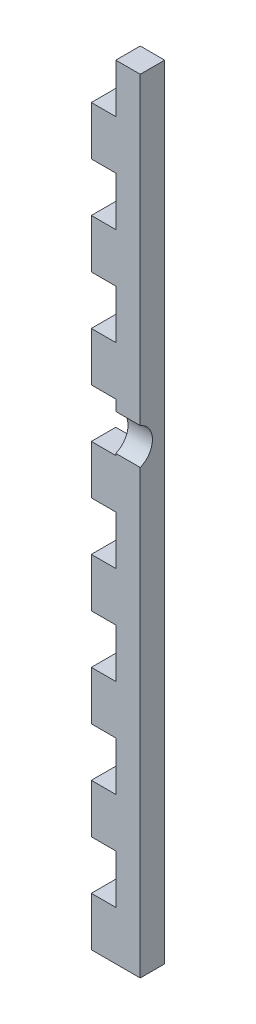
SolidWorks part; units mm, degrees
material "Balsa"
ref_plane "Alzado" through (0, 0, 0) normal (0, 0, 1) x (1, 0, 0)
ref_plane "Planta" through (0, 0, 0) normal (0, 1, 0) x (1, 0, 0)
ref_plane "Vista lateral" through (0, 0, 0) normal (1, 0, 0) x (0, 0, -1)
sketch "Croquis1" plane through (0, 0, 0) normal (0, 0, 1) x (1, 0, 0)
  line L0 (-10.5031, 53.1111) -> (-10.5031, 43.1111)
  line L1 (-10.5031, 73.1111) -> (-0.5031, 73.1111)
  line L2 (-10.5031, 73.1111) -> (-10.5031, -86.8889)
  line L3 (-10.5031, -86.8889) -> (-0.5031, -86.8889)
  line L4 (-0.5031, 73.1111) -> (-0.5031, -86.8889)
  line L5 (-10.5031, 73.1111) -> (-5.5031, 73.1111)
  line L6 (-10.5031, 73.1111) -> (-10.5031, 63.1111)
  line L7 (-10.5031, 63.1111) -> (-5.5031, 63.1111)
  line L8 (-5.5031, 73.1111) -> (-5.5031, 63.1111)
  line L9 (-10.5031, 53.1111) -> (-5.5031, 53.1111)
  line L10 (-5.5031, 53.1111) -> (-5.5031, 43.1111)
  line L11 (-10.5031, 43.1111) -> (-5.5031, 43.1111)
  line L12 (-10.5031, 33.1111) -> (-10.5031, 23.1111)
  line L13 (-10.5031, 33.1111) -> (-5.5031, 33.1111)
  line L14 (-5.5031, 33.1111) -> (-5.5031, 23.1111)
  line L15 (-10.5031, 23.1111) -> (-5.5031, 23.1111)
  line L16 (-10.5031, 13.1111) -> (-10.5031, 3.1111)
  line L17 (-10.5031, 13.1111) -> (-5.5031, 13.1111)
  line L18 (-5.5031, 13.1111) -> (-5.5031, 3.1111)
  line L19 (-10.5031, 3.1111) -> (-5.5031, 3.1111)
  line L20 (-10.5031, -6.8889) -> (-10.5031, -16.8889)
  line L21 (-10.5031, -6.8889) -> (-5.5031, -6.8889)
  line L22 (-5.5031, -6.8889) -> (-5.5031, -16.8889)
  line L23 (-10.5031, -16.8889) -> (-5.5031, -16.8889)
  line L24 (-10.5031, -26.8889) -> (-10.5031, -36.8889)
  line L25 (-10.5031, -26.8889) -> (-5.5031, -26.8889)
  line L26 (-5.5031, -26.8889) -> (-5.5031, -36.8889)
  line L27 (-10.5031, -36.8889) -> (-5.5031, -36.8889)
  line L28 (-10.5031, -46.8889) -> (-10.5031, -56.8889)
  line L29 (-10.5031, -46.8889) -> (-5.5031, -46.8889)
  line L30 (-5.5031, -46.8889) -> (-5.5031, -56.8889)
  line L31 (-10.5031, -56.8889) -> (-5.5031, -56.8889)
  line L32 (-10.5031, -66.8889) -> (-10.5031, -76.8889)
  line L33 (-10.5031, -66.8889) -> (-5.5031, -66.8889)
  line L34 (-5.5031, -66.8889) -> (-5.5031, -76.8889)
  line L35 (-10.5031, -76.8889) -> (-5.5031, -76.8889)
  dimension "D1" = 160
  dimension "D2" = 10
  dimension "D3" = 10
  dimension "D4" = 5
  dimension "D5" = 8
extrude "Saliente-Extruir1" add sketch "Croquis1" along normal blind 5 contours L35 L2 L3 L4 L1 L8 L7 L9 L10 L11 L13 L14 L15 L17 L18 L19 L21 L22 L23 L25 L26 L27 L29 L30 L31 L33 L34
sketch "Croquis3" plane through (-5.5031, 0, 0) normal (-1, 0, 0) x (0, 0, 1)
  line L0 (2.5, 15.0659) -> (2.5, -1.4555) construction
  line L2 (-4.0644, 10.6111) -> (10.726, 10.6111) construction
  line L3 (5, 13.1111) -> (5, 3.1111) construction
  line L4 (-3.6251, 3.7811) -> (10.4576, 3.7811) construction
  line L5 (-4.5282, 7.2011) -> (11.7999, 7.2011) construction
  line L6 (5, 13.1111) -> (0, 13.1111) construction
  line L7 (5, 3.1111) -> (0, 3.1111) construction
  circle A0 centre (6.5, 7.2011) radius 4
  point P16 (0, 0)
  dimension "D2" = 8
  dimension "D3" = 2.5
  dimension "D1" = 2.5
  dimension "D4" = 0.67
  dimension "D5" = 3.42
extrude "Cortar-Extruir1" cut sketch "Croquis3" against normal blind 5
